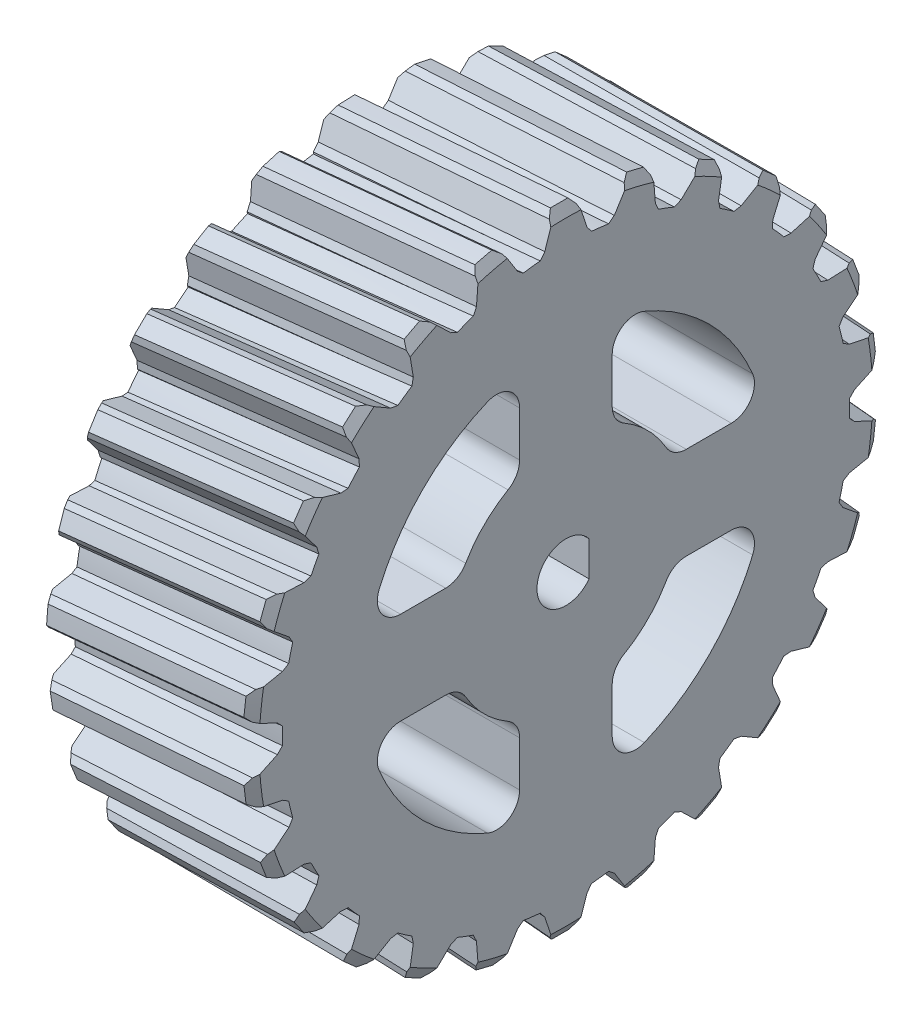
SolidWorks part; units mm, degrees
ref_plane "Front Plane" through (0, 0, 0) normal (0, 0, 1) x (1, 0, 0)
ref_plane "Top Plane" through (0, 0, 0) normal (0, 1, 0) x (1, 0, 0)
ref_plane "Right Plane" through (0, 0, 0) normal (1, 0, 0) x (0, 0, -1)
sketch "Sketch1" plane through (0, 0, 0) normal (1, 0, 0) x (0, 0, -1)
  line L0 (-4, 10.3923) -> (-4, 14.2916)
  line L5 (-14.2916, 4) -> (-10.3923, 4)
  line L6 (-14.2916, -4) -> (-10.3923, -4)
  line L11 (2, 1.5) -> (2, -1.5)
  line L12 (-2.5, 0) -> (-2.5, 6.582) construction
  line L13 (4, 10.3923) -> (4, 14.2916)
  line L14 (10.3923, 4) -> (14.2916, 4)
  line L15 (10.3923, -4) -> (14.2916, -4)
  line L16 (4, -14.2916) -> (4, -10.3923)
  line L17 (-4, -14.2916) -> (-4, -10.3923)
  circle A0 centre (0, 0) radius 24.5
  arc A1 (-6.7742, 16.1357) -> (-16.1357, 6.7742) centre (0, 0) ccw
  arc A2 (-5, 8.6603) -> (-8.6603, 5) centre (0, 0) ccw
  arc A3 (16.1357, 6.7742) -> (6.7742, 16.1357) centre (0, 0) ccw
  arc A4 (8.6603, 5) -> (5, 8.6603) centre (0, 0) ccw
  arc A5 (5, -8.6603) -> (8.6603, -5) centre (0, 0) ccw
  arc A6 (6.7742, -16.1357) -> (16.1357, -6.7742) centre (0, 0) ccw
  arc A7 (-16.1357, -6.7742) -> (-6.7742, -16.1357) centre (0, 0) ccw
  arc A8 (-8.6603, -5) -> (-5, -8.6603) centre (0, 0) ccw
  arc A9 (-8.6603, -5) -> (-10.3923, -4) centre (-10.3923, -6) ccw
  arc A10 (-14.2916, -4) -> (-16.1357, -6.7742) centre (-14.2916, -6) ccw
  arc A11 (-6.7742, -16.1357) -> (-4, -14.2916) centre (-6, -14.2916) ccw
  arc A12 (-4, -10.3923) -> (-5, -8.6603) centre (-6, -10.3923) ccw
  arc A13 (10.3923, -4) -> (8.6603, -5) centre (10.3923, -6) ccw
  arc A14 (4, -10.3923) -> (5, -8.6603) centre (6, -10.3923) cw
  arc A15 (6.7742, -16.1357) -> (4, -14.2916) centre (6, -14.2916) cw
  arc A16 (16.1357, -6.7742) -> (14.2916, -4) centre (14.2916, -6) ccw
  arc A17 (16.1357, 6.7742) -> (14.2916, 4) centre (14.2916, 6) cw
  arc A18 (10.3923, 4) -> (8.6603, 5) centre (10.3923, 6) cw
  arc A19 (5, 8.6603) -> (4, 10.3923) centre (6, 10.3923) cw
  arc A20 (6.7742, 16.1357) -> (4, 14.2916) centre (6, 14.2916) ccw
  arc A21 (-4, 14.2916) -> (-6.7742, 16.1357) centre (-6, 14.2916) ccw
  arc A22 (-14.2916, 4) -> (-16.1357, 6.7742) centre (-14.2916, 6) cw
  arc A23 (-8.6603, 5) -> (-10.3923, 4) centre (-10.3923, 6) cw
  arc A24 (-5, 8.6603) -> (-4, 10.3923) centre (-6, 10.3923) ccw
  arc A25 (2, 1.5) -> (2, -1.5) centre (0, 0) ccw
  point P9 (-9.1652, -4)
  point P22 (-17.0367, -4)
  point P33 (4, -9.1652)
  point P42 (9.1652, 4)
  dimension "D1" = 49
  dimension "D2" = 35
  dimension "D3" = 20
  dimension "D4" = 2
  dimension "D5" = 5
  dimension "D6" = 4.5
extrude "Boss-Extrude1" add sketch "Sketch1" along normal blind 18
sketch "Sketch2" plane through (18, 0, 0) normal (1, 0, 0) x (0, 0, -1)
  line L0 (0, 0) -> (0, 33.2044) construction
  line L1 (-1.1664, 26.8843) -> (-1.8254, 24.8951)
  line L2 (2.2785, 24.3258) -> (1.8254, 24.8951)
  line L3 (-1.1664, 26.8843) -> (-0.75, 27.389)
  line L4 (-2.25, 24.3616) -> (-1.8254, 24.8951)
  line L5 (1.1664, 26.8843) -> (1.8254, 24.8951)
  line L6 (1.1664, 26.8843) -> (0.75, 27.389)
  line L7 (-2.25, 24.3616) -> (-2.25, 23.3214)
  line L8 (2.2785, 24.3258) -> (2.2785, 23.3214)
  line L9 (-2.25, 23.3214) -> (2.2785, 23.3214)
  arc A0 (0.75, 27.389) -> (-0.75, 27.389) centre (0, -58.1077) ccw
sketch3d "3DSketch1"
  line L0 (18, 27.3923, 0) -> (-0.4296, 27.3923, 1.6124)
  line L1 (18, 0, 0) -> (18, 33.2044, 0) construction
  line L2 (18, 27.3923, 0) -> (18, 27.3923, -16.1227) construction
  arc A0 (18, 27.389, -0.75) -> (18, 27.389, 0.75) centre (18, -58.1077, 0) ccw construction
  point P5 (103.5, -58.1077, 0)
  point P9 (-2.5221, 27.3923, -10.5022)
  dimension "D1" = 95
  dimension "D2" = 18.5
  dimension "D3" = 90
sweep "Sweep1" add profiles "Sketch2" path "3DSketch1"
pattern_circular "CirPattern1" count 26 over 360 of "Sweep1"
sketch "Sketch4" plane through (0, 0, 0) normal (0, 1, 0) x (1, 0, 0)
  line L0 (0, 0) -> (48.1921, 0) construction
  line L1 (9, 0) -> (9, 37.1268) construction
  line L2 (18, 14.8413) -> (18, 26.5)
  line L3 (18, 26.5) -> (17.25, 27.75)
  line L4 (17.25, 27.75) -> (0.75, 27.75)
  line L5 (0.75, 27.75) -> (0, 26.5)
  line L6 (0, 26.5) -> (0, 14.8413)
  line L7 (0, 14.8413) -> (-8.1315, 14.8413)
  line L8 (-8.1315, 14.8413) -> (-8.1315, 41.8943)
  line L9 (-8.1315, 41.8943) -> (23.949, 41.8943)
  line L10 (23.949, 41.8943) -> (23.949, 14.8413)
  line L11 (23.949, 14.8413) -> (18, 14.8413)
  point P5 (0, 0)
  point P19 (-0.2189, 24.8598)
  point P20 (18, 23.1799)
  dimension "D1" = 9
  dimension "D2" = 16.5
  dimension "D3" = 53
  dimension "D4" = 55.5
  dimension "D5" = 53
revolve "Cut-Revolve1" cut sketch "Sketch4" angle 360 about L0
